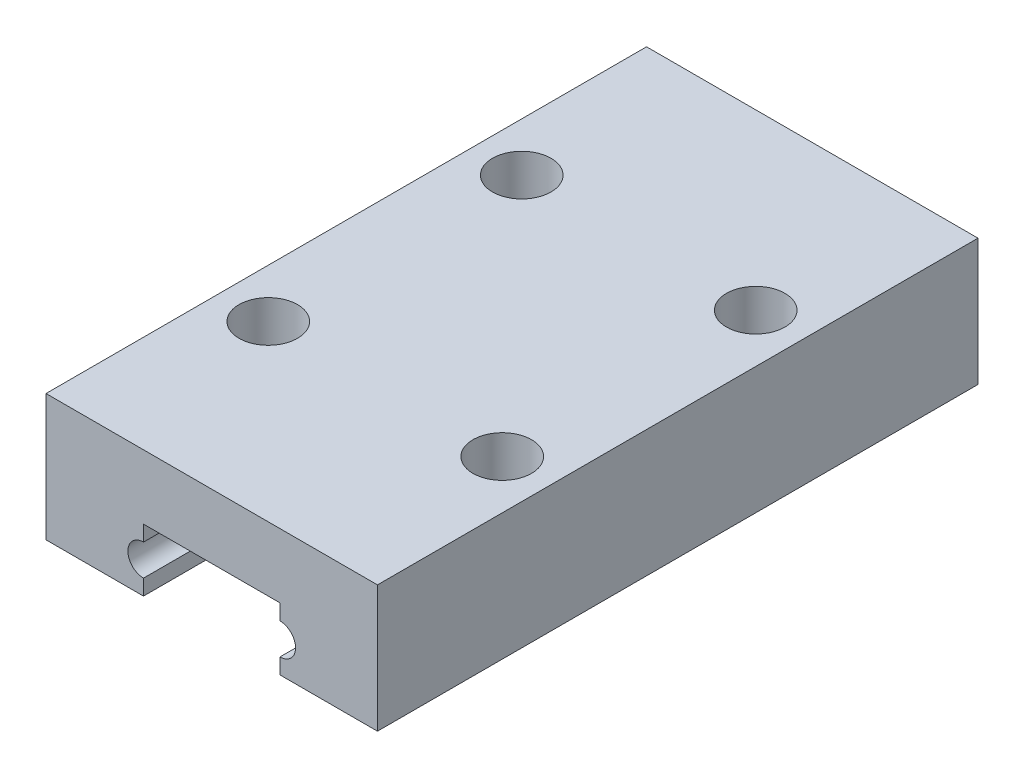
SolidWorks part; units mm, degrees
ref_plane "Plano frontal" through (0, 0, 0) normal (0, 0, 1) x (1, 0, 0)
ref_plane "Plano superior" through (0, 0, 0) normal (0, 1, 0) x (1, 0, 0)
ref_plane "Plano direito" through (0, 0, 0) normal (1, 0, 0) x (0, 0, -1)
sketch "Esboço1" plane through (0, 0, 0) normal (0, 0, 1) x (1, 0, 0)
  line L0 (-8.5, 6.5) -> (8.5, 6.5)
  line L1 (8.5, 6.5) -> (8.5, 0)
  line L2 (8.5, 0) -> (3.5, 0)
  line L3 (3.5, 0) -> (3.5, 0.8)
  line L7 (3.5, 2.4) -> (3.5, 3.2)
  line L8 (3.5, 3.2) -> (-3.5, 3.2)
  line L9 (0, 0) -> (0, 6.5) construction
  line L10 (3.3, 1.6) -> (3.7904, 1.6) construction
  line L11 (-3.5, 3.2) -> (-3.5, 2.4)
  line L16 (-3.5, 0) -> (-3.5, 0.8)
  line L17 (-8.5, 0) -> (-3.5, 0)
  line L18 (-8.5, 6.5) -> (-8.5, 0)
  arc A2 (3.5, 0.8) -> (3.5, 2.4) centre (3.5, 1.6) ccw
  arc A3 (-3.5, 0.8) -> (-3.5, 2.4) centre (-3.5, 1.6) cw
  point P17 (0, 3.2)
  dimension "D5" = 0.8
  dimension "D1" = 17
  dimension "D2" = 6.5
  dimension "D3" = 5
  dimension "D4" = 3.2
extrude "Ressalto-extrusão1" add sketch "Esboço1" along normal blind 30.8 contours L0 L1 L2 L3 A2 L7 L8 L11 A3 L16 L17 L18
sketch "Esboço2" plane through (0, 6.5, 0) normal (0, 1, 0) x (1, 0, 0)
  line L0 (0, 0) -> (0, -30.8) construction
  line L1 (-8.5, 0) -> (8.5, 0) construction
  line L2 (-8.5, -30.8) -> (8.5, -30.8) construction
  line L3 (0, -15.4) -> (8.5, -15.4) construction
  line L4 (8.5, -30.8) -> (8.5, 0) construction
  circle A0 centre (6, -21.9) radius 1.5
  circle A1 centre (6, -8.9) radius 1.5
  circle A3 centre (-6, -21.9) radius 1.5
  circle A4 centre (-6, -8.9) radius 1.5
  dimension "D2" = 13
  dimension "D3" = 3
  dimension "D1" = 12
extrude "Corte-extrusão1" cut sketch "Esboço2" against normal blind 30.8
